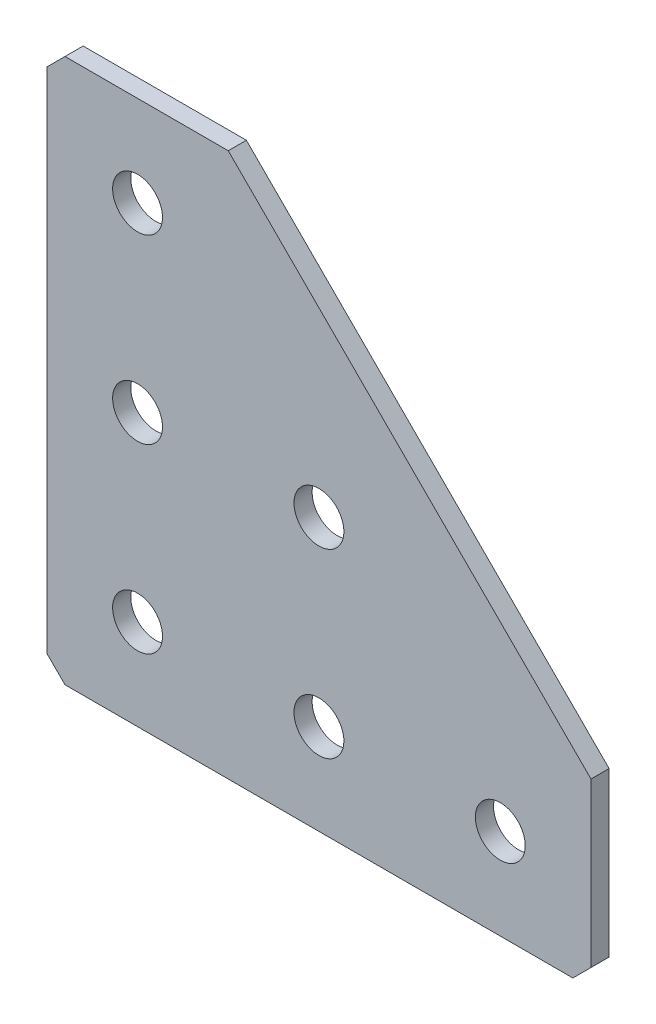
SolidWorks part; units mm, degrees
material "Простая углеродистая сталь"
ref_plane "Спереди(Плоскость XY)" through (0, 0, 0) normal (0, 0, 1) x (1, 0, 0)
ref_plane "Сверху(Плоскость XZ)" through (0, 0, 0) normal (0, 1, 0) x (1, 0, 0)
ref_plane "Справа(Плоскость ZY)" through (0, 0, 0) normal (1, 0, 0) x (0, 0, -1)
sketch "Эскиз1" plane through (0, 0, 0) normal (0, 0, -1) x (1, 0, 0)
  line L0 (0, 0) -> (0, 60)
  line L1 (0, 60) -> (60, 60)
  line L2 (60, 60) -> (60, 40)
  line L3 (60, 40) -> (20, 40) construction
  line L4 (20, 40) -> (20, 0) construction
  line L5 (20, 0) -> (0, 0)
  line L6 (20, 0) -> (60, 40)
  dimension "D1" = 60
  dimension "D3" = 20
extrude "Бобышка-Вытянуть1" add sketch "Эскиз1" along normal blind 2
hole_wizard "Отверстие с зазором M51" positions "Эскиз2" profile "Эскиз3" hole size "M5" standard "DIN" end condition through all
sketch "Эскиз2" plane through (0, 0, -2) normal (0, 0, -1) x (1, 0, 0)
  line L0 (10, 0) -> (10, 60) construction
  line L1 (0, 0) -> (20, 0) construction
  line L2 (60, 60) -> (0, 60) construction
  line L3 (60, 50) -> (0, 50) construction
  line L4 (60, 40) -> (60, 60) construction
  line L5 (0, 60) -> (0, 0) construction
  point P0 (30, 50)
  point P2 (10, 50)
  point P4 (10, 30)
  point P6 (10, 10)
  point P21 (50, 50)
  point P22 (30, 30)
  dimension "D1" = 20
  dimension "D2" = 20
  dimension "D3" = 20
  dimension "D4" = 10
  dimension "D5" = 20
sketch "Эскиз3" plane through (30, -50, -2) normal (1, 0, 0) x (0, 1, 0)
  line L0 (0, 0) -> (0, 2)
  line L1 (0, 2) -> (2.75, 2)
  line L2 (2.75, 2) -> (2.75, 0)
  line L5 (2.75, 0) -> (0, 0)
  line L11 (0, -6.35) -> (0, 107.95) construction
  dimension "Диаметр сквозного отверстия" = 5.5
  dimension "Глубина сквозного отверстия" = 2
chamfer "Фаска1" distance 2 angle 45 3 edges at (0, 0, -1) (60, -60, -1) (0, -60, -1)
